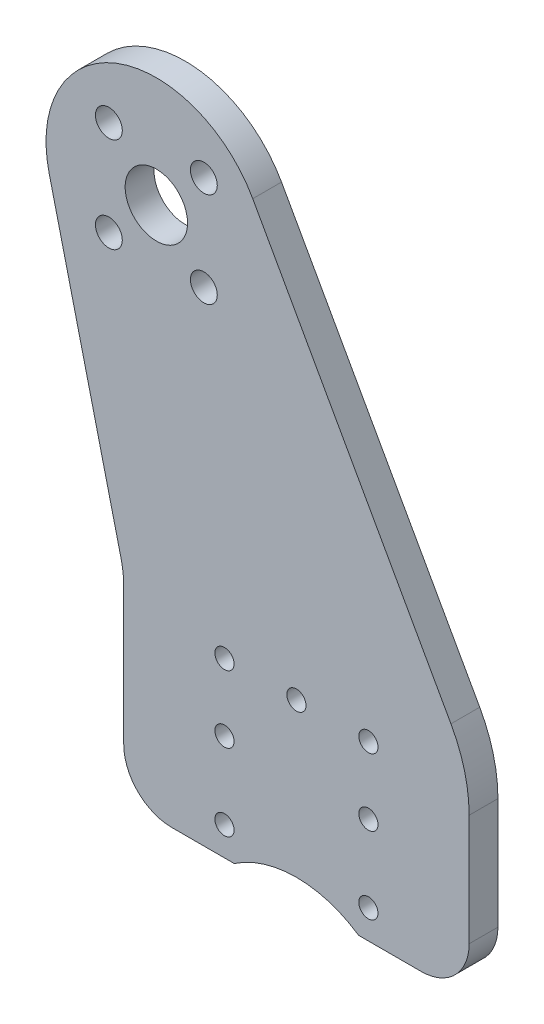
SolidWorks part; units mm, degrees
ref_plane "Спереди" through (0, 0, 0) normal (0, 0, 1) x (1, 0, 0)
ref_plane "Сверху" through (0, 0, 0) normal (0, 1, 0) x (1, 0, 0)
ref_plane "Справа" through (0, 0, 0) normal (1, 0, 0) x (0, 0, -1)
sketch "Эскиз1" plane through (0, 0, 0) normal (0, 0, 1) x (1, 0, 0)
  line L0 (0, 0) -> (0, -64.8775) construction
  line L1 (-4.9497, 4.9497) -> (4.9497, 4.9497) construction
  line L2 (-4.9497, 4.9497) -> (-4.9497, -4.9497) construction
  line L3 (-4.9497, -4.9497) -> (4.9497, -4.9497) construction
  line L4 (4.9497, 4.9497) -> (4.9497, -4.9497) construction
  line L5 (-4.9497, 4.9497) -> (4.9497, -4.9497) construction
  line L6 (-4.9497, -4.9497) -> (4.9497, 4.9497) construction
  line L7 (0, -64.8775) -> (14.6, -64.8775) construction
  line L8 (24.6, -34.8775) -> (4.6, -34.8775) construction
  line L9 (24.6, -34.8775) -> (24.6, -74.8775) construction
  line L10 (4.6, -34.8775) -> (4.6, -74.8775) construction
  line L11 (4.6, -74.8775) -> (24.6, -74.8775) construction
  line L12 (1.6, -55.3775) -> (8.1193, -55.3775)
  line L13 (21.0807, -55.3775) -> (27.6, -55.3775)
  line L14 (-3.4, -36.069) -> (-3.4, -50.3775)
  line L15 (-3.68, -33.7193) -> (-11.178, -2.7022)
  line L16 (32.6, -38.7747) -> (32.6, -50.3775)
  line L17 (30.703, -31.4732) -> (10.0456, 5.5978)
  circle A0 centre (0, 0) radius 3.25
  circle A1 centre (-4.9497, 4.9497) radius 1.4
  circle A2 centre (4.9497, 4.9497) radius 1.4
  circle A3 centre (4.9497, -4.9497) radius 1.4
  circle A4 centre (-4.9497, -4.9497) radius 1.4
  circle A5 centre (0, 0) radius 10 construction
  circle A6 centre (7.1, -37.3775) radius 1
  circle A7 centre (22.1, -37.3775) radius 1
  circle A8 centre (7.1, -52.3775) radius 1
  circle A9 centre (22.1, -52.3775) radius 1
  arc A10 (10.0456, 5.5978) -> (-11.178, -2.7022) centre (0, 0) ccw
  circle A11 centre (14.6, -64.8775) radius 10 construction
  circle A12 centre (14.6, -37.3775) radius 1
  circle A13 centre (22.1, -44.3775) radius 1
  circle A14 centre (7.1, -44.3775) radius 1
  arc A15 (21.0807, -55.3775) -> (8.1193, -55.3775) centre (14.6, -64.8775) ccw
  arc A16 (32.6, -50.3775) -> (27.6, -55.3775) centre (27.6, -50.3775) cw
  arc A17 (1.6, -55.3775) -> (-3.4, -50.3775) centre (1.6, -50.3775) cw
  arc A18 (32.6, -38.7747) -> (30.703, -31.4732) centre (17.6, -38.7747) ccw
  arc A19 (-3.4, -36.069) -> (-3.68, -33.7193) centre (-13.4, -36.069) ccw
  point P3 (0, 0)
  point P47 (-3.4, -55.3775)
  point P50 (32.6, -34.8775)
  point P53 (-3.4, -34.8775)
  dimension "D1" = 6.5
  dimension "D3" = 2.8
  dimension "D6" = 20
  dimension "D9" = 2
  dimension "D15" = 23
  dimension "D16" = 10
  dimension "D17" = 23
  dimension "D21" = 5
  dimension "D22" = 15
  dimension "D23" = 10
  dimension "D2" = 14
  dimension "D4" = 66.5
  dimension "D5" = 14.6
  dimension "D7" = 27.5
  dimension "D8" = 7.5
  dimension "D10" = 15
  dimension "D11" = 15
  dimension "D12" = 30
  dimension "D13" = 20
  dimension "D14" = 40
  dimension "D18" = 3
  dimension "D19" = 7
  dimension "D20" = 8
extrude "Бобышка-Вытянуть1" add sketch "Эскиз1" against normal blind 3
